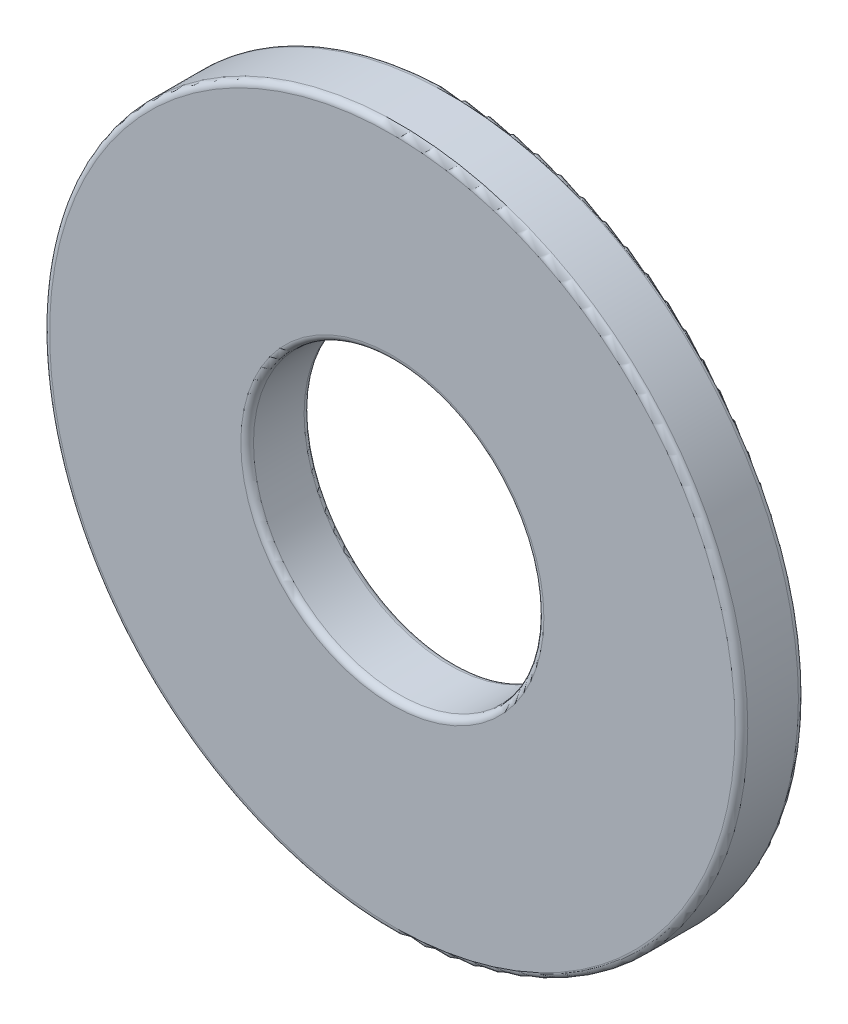
SolidWorks part; units mm, degrees
material "AISI 1020"
ref_plane "Front Plane" through (0, 0, 0) normal (0, 0, 1) x (1, 0, 0)
ref_plane "Top Plane" through (0, 0, 0) normal (0, 1, 0) x (1, 0, 0)
ref_plane "Right Plane" through (0, 0, 0) normal (1, 0, 0) x (0, 0, -1)
sketch "Sketch1" plane through (0, 0, 0) normal (0, 0, 1) x (1, 0, 0)
  circle A0 centre (0, 0) radius 9.525 construction
  circle A1 centre (0, 0) radius 3.9624 construction
  dimension "OD" = 19.05
  dimension "ID" = 7.9248
sketch "Sketch2" plane through (0, 0, 0) normal (1, 0, 0) x (0, 0, -1)
  line L0 (-0.8636, -9.525) -> (0.8636, -9.525) construction
  point P0 (0.6096, -9.525)
  point P4 (0, -9.525)
  dimension "Thickness Max" = 1.7272
  dimension "Thickness Min" = 1.4732
sketch "Sketch3" plane through (0, 0, 0) normal (0, 0, 1) x (1, 0, 0)
  circle A0 centre (0, 0) radius 9.525 construction
  circle A1 centre (0, 0) radius 9.525
  circle A2 centre (0, 0) radius 3.9624 construction
  circle A3 centre (0, 0) radius 3.9624
extrude "Boss-Extrude1" add sketch "Sketch3" against normal up to vertex (0.8636 mm away) and the other way up to vertex (0.8636 mm away) up to point (0, -9.525, -0.8636) other way up to point (0, -9.525, 0.8636)
fillet "Fillet1" radius 0.1727 4 edges at (9.525, 0, -0.8636) (3.9624, 0, -0.8636) (3.9624, 0, 0.8636) (9.525, 0, 0.8636)
equation "\"D1@Fillet1\" = \"Thickness Max@Sketch2\" * 0.1"
